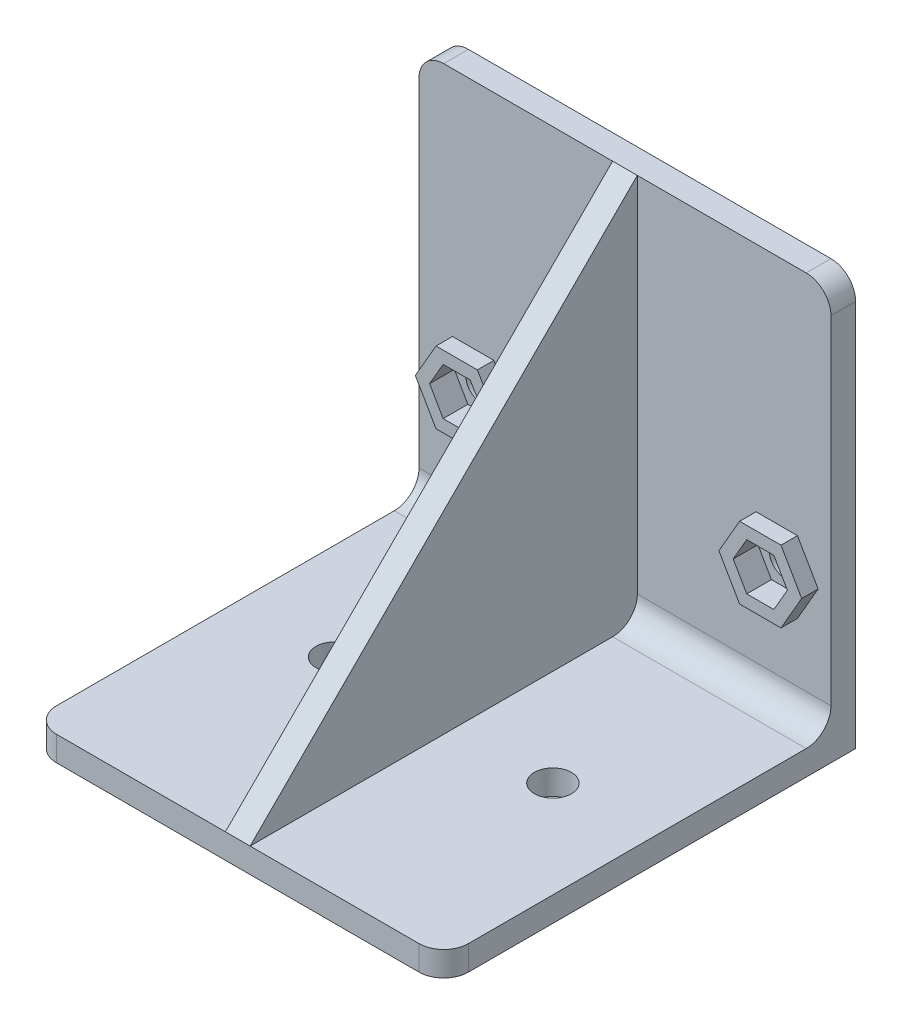
SolidWorks part; units mm, degrees
ref_plane "Front Plane" through (0, 0, 0) normal (0, 0, 1) x (1, 0, 0)
ref_plane "Top Plane" through (0, 0, 0) normal (0, 1, 0) x (1, 0, 0)
ref_plane "Right Plane" through (0, 0, 0) normal (1, 0, 0) x (0, 0, -1)
sketch "Sketch1" plane through (0, 0, 0) normal (0, 1, 0) x (1, 0, 0)
  line L1 (-25, 25) -> (25, 25)
  line L2 (-25, 25) -> (-25, -25)
  line L3 (-25, -25) -> (25, -25)
  line L4 (25, 25) -> (25, -25)
  line L5 (-25, 25) -> (25, -25) construction
  line L6 (-25, -25) -> (25, 25) construction
  point P0 (0, 0)
  dimension "D1" = 50
  dimension "D2" = 50
extrude "Boss-Extrude1" add sketch "Sketch1" along normal blind 3
sketch "Sketch2" plane through (0, 3, 0) normal (0, 1, 0) x (1, 0, 0)
  line L0 (25, -25) -> (25, 25) construction
  line L1 (-25, 25) -> (25, 25)
  line L2 (-25, 25) -> (-25, 22)
  line L3 (-25, 22) -> (25, 22)
  line L4 (25, 25) -> (25, 22)
  dimension "D1" = 3
extrude "Boss-Extrude2" add sketch "Sketch2" along normal offset from surface (47 mm away) 50 up to face at (0, 0, 0)
ref_plane "Plane1" through (0, 0, 0) normal (1, 0, 0) x (0, 0, -1)
sketch "Sketch3" plane through (0, 0, 0) normal (1, 0, 0) x (0, 0, -1)
  line L0 (-25, 3) -> (22, 50)
  line L1 (22, 50) -> (22, 3)
  line L2 (22, 3) -> (-25, 3)
extrude "Boss-Extrude3" add sketch "Sketch3" along normal mid plane 3
sketch "Sketch4" plane through (0, 0, -25) normal (0, 0, -1) x (-1, 0, 0)
  line L0 (9.5, 11.25) -> (9.5, 18.75) construction
  line L1 (13.25, 11.25) -> (5.75, 11.25)
  line L2 (13.25, 11.25) -> (13.25, 18.75)
  line L3 (13.25, 18.75) -> (5.75, 18.75)
  line L4 (5.75, 11.25) -> (5.75, 18.75)
  line L5 (25, 50) -> (25, 0) construction
  line L6 (13.25, 15) -> (5.75, 15) construction
  line L7 (-25, 0) -> (25, 0) construction
  line L8 (0, 50) -> (0, 0) construction
  line L9 (-25, 50) -> (25, 50) construction
  line L10 (-25, 17.5) -> (25, 17.5) construction
  line L11 (-25, 50) -> (-25, 0) construction
  circle A0 centre (-18.425, 17.5) radius 1.9
  circle A1 centre (18.425, 17.5) radius 1.9
  dimension "D5" = 36.85
  dimension "D6" = 3.8
  dimension "D1" = 15.5
  dimension "D2" = 15
  dimension "D4" = 7.5
  dimension "D7" = 17.5
extrude "Cut-Extrude1" cut sketch "Sketch4" against normal up to next
fillet "Fillet1" radius 1 4 edges at (-5.75, 11.25, -23.5) (-13.25, 11.25, -23.5) (-13.25, 18.75, -23.5) (-5.75, 18.75, -23.5)
sketch "Sketch5" plane through (-1.5, 0, 0) normal (-1, 0, 0) x (0, 0, 1)
  line L6 (-19, 6) -> (17.7574, 6)
  line L7 (17.7574, 6) -> (-19, 42.7574)
  line L8 (-19, 42.7574) -> (-19, 6)
  line L9 (-19, 6) -> (17.7574, 6)
  line L10 (17.7574, 6) -> (-19, 42.7574)
  line L11 (-19, 42.7574) -> (-19, 6)
  dimension "D1" = 3
sketch "Sketch6" plane through (0, 0, -22) normal (0, 0, 1) x (1, 0, 0)
  line L0 (1.5, 3) -> (25, 3) construction
  line L1 (16.7796, 14.65) -> (20.0704, 14.65)
  line L2 (20.0704, 14.65) -> (21.7159, 17.5)
  line L3 (21.7159, 17.5) -> (20.0704, 20.35)
  line L4 (20.0704, 20.35) -> (16.7796, 20.35)
  line L5 (16.7796, 20.35) -> (15.1341, 17.5)
  line L6 (15.1341, 17.5) -> (16.7796, 14.65)
  line L7 (0, 50) -> (0, 0) construction
  line L8 (1.5, 50) -> (-1.5, 50) construction
  line L9 (-20.0704, 14.65) -> (-21.7159, 17.5)
  line L10 (-21.7159, 17.5) -> (-20.0704, 20.35)
  line L11 (-20.0704, 20.35) -> (-16.7796, 20.35)
  line L12 (-16.7796, 20.35) -> (-15.1341, 17.5)
  line L13 (-15.1341, 17.5) -> (-16.7796, 14.65)
  line L14 (-16.7796, 14.65) -> (-20.0704, 14.65)
  circle A0 centre (18.425, 17.5) radius 2.85 construction
  dimension "D1" = 5.7
extrude "Cut-Extrude3" cut sketch "Sketch6" against normal blind 1
sketch "Sketch7" plane through (0, 0, -22) normal (0, 0, 1) x (1, 0, 0)
  line L0 (-13.25, 17.75) -> (-13.25, 12.25) construction
  line L1 (-13.25, 17.75) -> (-13.25, 12.25)
  line L48 (-15.9135, 13.15) -> (-13.4021, 17.5)
  line L49 (-20.9365, 13.15) -> (-15.9135, 13.15)
  line L50 (-23.4479, 17.5) -> (-20.9365, 13.15)
  line L51 (-20.9365, 21.85) -> (-23.4479, 17.5)
  line L52 (-15.9135, 21.85) -> (-20.9365, 21.85)
  line L53 (-13.4021, 17.5) -> (-15.9135, 21.85)
  line L54 (-15.9135, 13.15) -> (-13.4021, 17.5)
  line L55 (-20.9365, 13.15) -> (-15.9135, 13.15)
  line L56 (-23.4479, 17.5) -> (-20.9365, 13.15)
  line L57 (-20.9365, 21.85) -> (-23.4479, 17.5)
  line L58 (-15.9135, 21.85) -> (-20.9365, 21.85)
  line L59 (-13.4021, 17.5) -> (-15.9135, 21.85)
  line L66 (13.4021, 17.5) -> (15.9135, 13.15)
  line L67 (15.9135, 13.15) -> (20.9365, 13.15)
  line L68 (20.9365, 13.15) -> (23.4479, 17.5)
  line L69 (23.4479, 17.5) -> (20.9365, 21.85)
  line L70 (20.9365, 21.85) -> (15.9135, 21.85)
  line L71 (15.9135, 21.85) -> (13.4021, 17.5)
  line L72 (13.4021, 17.5) -> (15.9135, 13.15)
  line L73 (15.9135, 13.15) -> (20.9365, 13.15)
  line L74 (20.9365, 13.15) -> (23.4479, 17.5)
  line L75 (23.4479, 17.5) -> (20.9365, 21.85)
  line L76 (20.9365, 21.85) -> (15.9135, 21.85)
  line L77 (15.9135, 21.85) -> (13.4021, 17.5)
  line L79 (-16.7796, 14.65) -> (-15.1341, 17.5)
  line L80 (-20.0704, 14.65) -> (-16.7796, 14.65)
  line L81 (-21.7159, 17.5) -> (-20.0704, 14.65)
  line L82 (-20.0704, 20.35) -> (-21.7159, 17.5)
  line L83 (-16.7796, 20.35) -> (-20.0704, 20.35)
  line L84 (-15.1341, 17.5) -> (-16.7796, 20.35)
  line L85 (-16.7796, 14.65) -> (-15.1341, 17.5)
  line L86 (-20.0704, 14.65) -> (-16.7796, 14.65)
  line L87 (-21.7159, 17.5) -> (-20.0704, 14.65)
  line L88 (-20.0704, 20.35) -> (-21.7159, 17.5)
  line L89 (-16.7796, 20.35) -> (-20.0704, 20.35)
  line L90 (-15.1341, 17.5) -> (-16.7796, 20.35)
  line L92 (16.7796, 14.65) -> (20.0704, 14.65)
  line L93 (15.1341, 17.5) -> (16.7796, 14.65)
  line L94 (16.7796, 20.35) -> (15.1341, 17.5)
  line L95 (20.0704, 20.35) -> (16.7796, 20.35)
  line L96 (21.7159, 17.5) -> (20.0704, 20.35)
  line L97 (20.0704, 14.65) -> (21.7159, 17.5)
  line L98 (16.7796, 14.65) -> (20.0704, 14.65)
  line L99 (15.1341, 17.5) -> (16.7796, 14.65)
  line L100 (16.7796, 20.35) -> (15.1341, 17.5)
  line L101 (20.0704, 20.35) -> (16.7796, 20.35)
  line L102 (21.7159, 17.5) -> (20.0704, 20.35)
  line L103 (20.0704, 14.65) -> (21.7159, 17.5)
  line M13 (-15.1341, 17.5) -> (-16.7796, 14.65)
  line M14 (-16.7796, 14.65) -> (-20.0704, 14.65)
  line M15 (-20.0704, 14.65) -> (-21.7159, 17.5)
  line M16 (-21.7159, 17.5) -> (-20.0704, 20.35)
  line M17 (-20.0704, 20.35) -> (-16.7796, 20.35)
  line M18 (-16.7796, 20.35) -> (-15.1341, 17.5)
  dimension "D1" = 1.5
  dimension "D2" = 1.5
  dimension "D3" = 0
  dimension "D4" = 0
extrude "Boss-Extrude4" add sketch "Sketch7" along normal blind 2 contours L76 L77 L72 L73 L74 L75 L103 L98 L99 L100 L101 L102 | L1 L59 L58 L57 L56 L55 L54 M18 M13 M14 M15 M16 M17
fillet "Fillet3" radius 3 6 edges at (13.25, 3, -22) (-13.25, 3, -22) (25, 1.5, 25) (-25, 1.5, 25) (25, 50, -23.5) (-25, 50, -23.5)
sketch "Sketch8" plane through (0, 3, 0) normal (0, 1, 0) x (1, 0, 0)
  line L0 (-25, 0) -> (25, 0) construction
  line L1 (-25, 19) -> (-25, -22) construction
  line L2 (25, -22) -> (25, 19) construction
  line L3 (-1.5, 0.6213) -> (-25, 0.6213) construction
  line L4 (-1.5, 19) -> (-1.5, -17.7574) construction
  line L5 (-13.25, 0.6213) -> (-13.25, 0) construction
  line L6 (0, 25) -> (0, -25) construction
  line L7 (22, 25) -> (-22, 25) construction
  line L8 (1.5, -25) -> (-1.5, -25) construction
  circle A0 centre (-13.25, 0) radius 2.25
  circle A1 centre (13.25, 0) radius 2.25
  dimension "D1" = 4.5
extrude "Cut-Extrude4" cut sketch "Sketch8" against normal up to next
